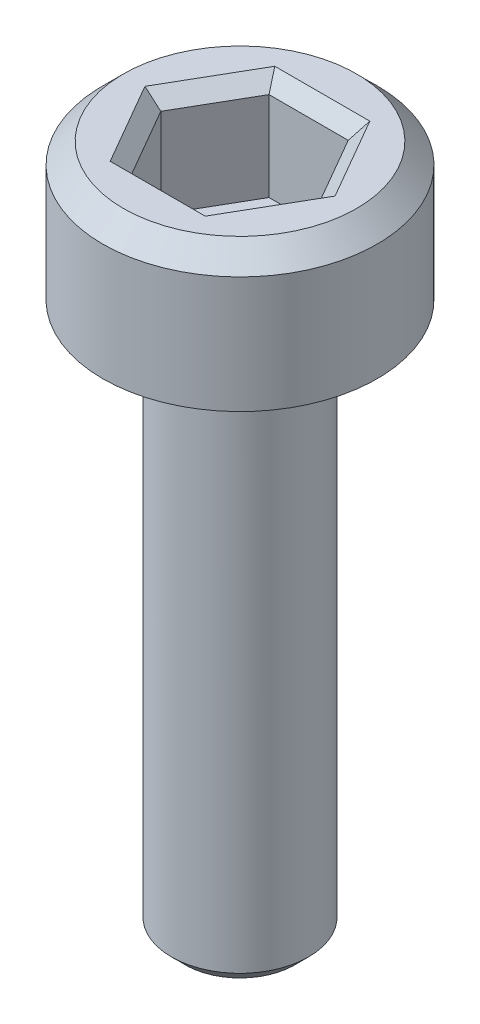
SolidWorks part; units mm, degrees
ref_plane "Front Plane" through (0, 0, 0) normal (0, 0, 1) x (1, 0, 0)
ref_plane "Top Plane" through (0, 0, 0) normal (0, 1, 0) x (1, 0, 0)
ref_plane "Right Plane" through (0, 0, 0) normal (1, 0, 0) x (0, 0, -1)
sketch "Sketch1" plane through (0, 0, 0) normal (0, 1, 0) x (1, 0, 0)
  circle A0 centre (0, 0) radius 2
  dimension "D1" = 4
extrude "Boss-Extrude1" add sketch "Sketch1" along normal blind 2
chamfer "Chamfer1" distance 0.3 angle 45 1 edges at (0, 2, 2)
sketch "Sketch2" plane through (0, 2, 0) normal (0, 1, 0) x (1, 0, 0)
  line L1 (1.1547, 0) -> (0.5774, 1)
  line L2 (0.5774, 1) -> (-0.5774, 1)
  line L3 (-0.5774, 1) -> (-1.1547, 0)
  line L4 (-1.1547, 0) -> (-0.5774, -1)
  line L5 (-0.5774, -1) -> (0.5774, -1)
  line L6 (0.5774, -1) -> (1.1547, 0)
  circle A0 centre (0, 0) radius 1 construction
  dimension "D1" = 2
extrude "Cut-Extrude1" cut sketch "Sketch2" against normal blind 1.5
chamfer "Chamfer2" distance 0.2 angle 45 6 edges at (0.866, 2, -0.5) (0.866, 2, 0.5) (0, 2, 1) (-0.866, 2, 0.5) (-0.866, 2, -0.5) (0, 2, -1)
sketch "Sketch3" plane through (0, 0, 0) normal (0, -1, 0) x (1, 0, 0)
  circle A0 centre (0, 0) radius 1
  dimension "D1" = 2
extrude "Boss-Extrude2" add sketch "Sketch3" along normal blind 8
chamfer "Chamfer3" distance 0.2 angle 45 1 edges at (0, -8, -1)
